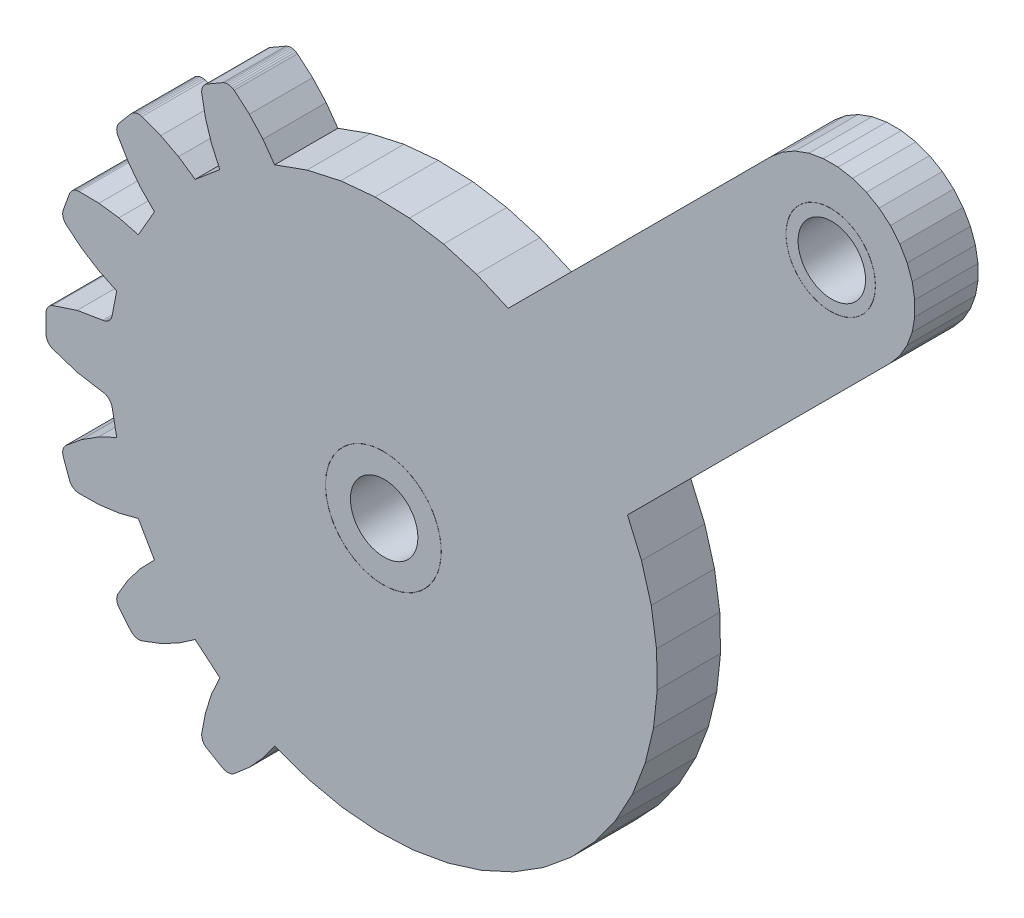
SolidWorks part; units mm, degrees
ref_plane "Front Plane" through (0, 0, 0) normal (0, 0, 1) x (1, 0, 0)
ref_plane "Top Plane" through (0, 0, 0) normal (0, 1, 0) x (1, 0, 0)
ref_plane "Right Plane" through (0, 0, 0) normal (1, 0, 0) x (0, 0, -1)
ref_plane "Plane1" through (0, 0, 3) normal (0, 0, 1) x (1, 0, 0)
sketch "Sketch1" plane through (0, 0, 3) normal (0, 0, 1) x (1, 0, 0)
  line L0 (41.2418, 13.6583) -> (41.2, 14.1358)
  line L1 (41.2, 14.1358) -> (41.2418, 14.6133)
  line L2 (41.2418, 14.6133) -> (41.3658, 15.0764)
  line L3 (41.3658, 15.0764) -> (41.5684, 15.5108)
  line L4 (41.5684, 15.5108) -> (41.8434, 15.9035)
  line L5 (41.8434, 15.9035) -> (42.1823, 16.2424)
  line L6 (42.1823, 16.2424) -> (42.575, 16.5174)
  line L7 (42.575, 16.5174) -> (43.0094, 16.72)
  line L8 (43.0094, 16.72) -> (43.4725, 16.844)
  line L9 (43.4725, 16.844) -> (43.95, 16.8858)
  line L10 (43.95, 16.8858) -> (44.4275, 16.844)
  line L11 (44.4275, 16.844) -> (44.8906, 16.72)
  line L12 (44.8906, 16.72) -> (45.325, 16.5174)
  line L13 (45.325, 16.5174) -> (45.7177, 16.2424)
  line L14 (45.7177, 16.2424) -> (46.0566, 15.9035)
  line L15 (46.0566, 15.9035) -> (46.3316, 15.5108)
  line L16 (46.3316, 15.5108) -> (46.5342, 15.0764)
  line L17 (46.5342, 15.0764) -> (46.6582, 14.6133)
  line L18 (46.6582, 14.6133) -> (46.7, 14.1358)
  line L19 (46.7, 14.1358) -> (46.6582, 13.6583)
  line L20 (46.6582, 13.6583) -> (46.5342, 13.1953)
  line L21 (46.5342, 13.1953) -> (46.3316, 12.7608)
  line L22 (46.3316, 12.7608) -> (46.0566, 12.3681)
  line L23 (46.0566, 12.3681) -> (45.7177, 12.0292)
  line L24 (45.7177, 12.0292) -> (45.325, 11.7542)
  line L25 (45.325, 11.7542) -> (44.8906, 11.5517)
  line L26 (44.8906, 11.5517) -> (44.4275, 11.4276)
  line L27 (44.4275, 11.4276) -> (43.95, 11.3858)
  line L28 (43.95, 11.3858) -> (43.4725, 11.4276)
  line L29 (43.4725, 11.4276) -> (43.0094, 11.5517)
  line L30 (43.0094, 11.5517) -> (42.575, 11.7542)
  line L31 (42.575, 11.7542) -> (42.1823, 12.0292)
  line L32 (42.1823, 12.0292) -> (41.8434, 12.3681)
  line L33 (41.8434, 12.3681) -> (41.5684, 12.7608)
  line L34 (41.5684, 12.7608) -> (41.3658, 13.1953)
  line L35 (41.3658, 13.1953) -> (41.2418, 13.6583)
  line L36 (30.938, 12.5267) -> (30.9937, 12.4646)
  line L37 (30.9937, 12.4646) -> (31.0383, 12.3942)
  line L38 (31.0383, 12.3942) -> (31.0705, 12.3173)
  line L39 (31.0705, 12.3173) -> (31.0896, 12.2361)
  line L40 (31.0896, 12.2361) -> (31.3026, 11.1288)
  line L41 (31.3026, 11.1288) -> (30.4429, 10.7165)
  line L42 (30.4429, 10.7165) -> (29.6383, 10.2049)
  line L43 (29.6383, 10.2049) -> (28.9004, 9.6011)
  line L44 (28.9004, 9.6011) -> (28.8438, 9.5394)
  line L45 (28.8438, 9.5394) -> (28.7983, 9.469)
  line L46 (28.7983, 9.469) -> (28.7652, 9.392)
  line L47 (28.7652, 9.392) -> (28.7454, 9.3106)
  line L48 (28.7454, 9.3106) -> (28.7395, 9.227)
  line L49 (28.7395, 9.227) -> (28.7477, 9.1436)
  line L50 (28.7477, 9.1436) -> (28.7696, 9.0627)
  line L51 (28.7696, 9.0627) -> (29.0602, 8.2643)
  line L52 (29.0602, 8.2643) -> (29.0954, 8.1882)
  line L53 (29.0954, 8.1882) -> (29.1427, 8.1191)
  line L54 (29.1427, 8.1191) -> (29.201, 8.0588)
  line L55 (29.201, 8.0588) -> (29.2685, 8.0092)
  line L56 (29.2685, 8.0092) -> (29.3433, 7.9715)
  line L57 (29.3433, 7.9715) -> (29.4234, 7.9468)
  line L58 (29.4234, 7.9468) -> (29.5065, 7.9358)
  line L59 (29.5065, 7.9358) -> (30.4599, 7.9477)
  line L60 (30.4599, 7.9477) -> (31.405, 8.0729)
  line L61 (31.405, 8.0729) -> (32.3286, 8.3097)
  line L62 (32.3286, 8.3097) -> (33.0938, 6.9844)
  line L63 (33.0938, 6.9844) -> (32.4269, 6.303)
  line L64 (32.4269, 6.303) -> (31.8459, 5.547)
  line L65 (31.8459, 5.547) -> (31.3589, 4.7273)
  line L66 (31.3589, 4.7273) -> (31.3269, 4.6499)
  line L67 (31.3269, 4.6499) -> (31.3082, 4.5682)
  line L68 (31.3082, 4.5682) -> (31.3034, 4.4846)
  line L69 (31.3034, 4.4846) -> (31.3127, 4.4013)
  line L70 (31.3127, 4.4013) -> (31.3357, 4.3207)
  line L71 (31.3357, 4.3207) -> (31.3719, 4.2451)
  line L72 (31.3719, 4.2451) -> (31.4202, 4.1766)
  line L73 (31.4202, 4.1766) -> (31.9664, 3.5258)
  line L74 (31.9664, 3.5258) -> (32.0254, 3.4663)
  line L75 (32.0254, 3.4663) -> (32.0936, 3.4176)
  line L76 (32.0936, 3.4176) -> (32.1689, 3.3809)
  line L77 (32.1689, 3.3809) -> (32.2493, 3.3573)
  line L78 (32.2493, 3.3573) -> (32.3325, 3.3474)
  line L79 (32.3325, 3.3474) -> (32.4162, 3.3517)
  line L80 (32.4162, 3.3517) -> (32.4981, 3.3698)
  line L81 (32.4981, 3.3698) -> (33.3899, 3.707)
  line L82 (33.3899, 3.707) -> (34.2352, 4.1479)
  line L83 (34.2352, 4.1479) -> (35.0221, 4.6863)
  line L84 (35.0221, 4.6863) -> (36.1944, 3.7027)
  line L85 (36.1944, 3.7027) -> (35.8008, 2.8342)
  line L86 (35.8008, 2.8342) -> (35.5134, 1.9252)
  line L87 (35.5134, 1.9252) -> (35.3361, 0.9883)
  line L88 (35.3361, 0.9883) -> (35.3325, 0.9046)
  line L89 (35.3325, 0.9046) -> (35.3429, 0.8215)
  line L90 (35.3429, 0.8215) -> (35.367, 0.7412)
  line L91 (35.367, 0.7412) -> (35.4042, 0.6661)
  line L92 (35.4042, 0.6661) -> (35.4534, 0.5983)
  line L93 (35.4534, 0.5983) -> (35.5133, 0.5396)
  line L94 (35.5133, 0.5396) -> (35.5821, 0.4918)
  line L95 (35.5821, 0.4918) -> (36.3179, 0.067)
  line L96 (36.3179, 0.067) -> (36.3937, 0.0313)
  line L97 (36.3937, 0.0313) -> (36.4745, 0.0088)
  line L98 (36.4745, 0.0088) -> (36.5578, 0.0001)
  line L99 (36.5578, 0.0001) -> (36.6414, 0.0054)
  line L100 (36.6414, 0.0054) -> (36.723, 0.0247)
  line L101 (36.723, 0.0247) -> (36.8002, 0.0572)
  line L102 (36.8002, 0.0572) -> (36.8709, 0.1022)
  line L103 (36.8709, 0.1022) -> (37.5936, 0.7242)
  line L104 (37.5936, 0.7242) -> (38.2371, 1.4276)
  line L105 (38.2371, 1.4276) -> (38.7925, 2.2027)
  line L106 (38.7925, 2.2027) -> (40.3707, 1.6383)
  line L107 (40.3707, 1.6383) -> (42.0084, 1.2816)
  line L108 (42.0084, 1.2816) -> (43.6784, 1.1386)
  line L109 (43.6784, 1.1386) -> (45.3529, 1.2117)
  line L110 (45.3529, 1.2117) -> (47.0041, 1.4996)
  line L111 (47.0041, 1.4996) -> (48.6045, 1.9976)
  line L112 (48.6045, 1.9976) -> (50.1275, 2.6974)
  line L113 (50.1275, 2.6974) -> (51.5479, 3.5872)
  line L114 (51.5479, 3.5872) -> (52.8419, 4.6525)
  line L115 (52.8419, 4.6525) -> (53.9882, 5.8754)
  line L116 (53.9882, 5.8754) -> (54.9676, 7.2356)
  line L117 (54.9676, 7.2356) -> (55.7638, 8.7105)
  line L118 (55.7638, 8.7105) -> (56.3636, 10.2755)
  line L119 (56.3636, 10.2755) -> (56.7571, 11.9048)
  line L120 (56.7571, 11.9048) -> (56.9377, 13.5711)
  line L121 (56.9377, 13.5711) -> (56.9024, 15.2469)
  line L122 (56.9024, 15.2469) -> (56.6518, 16.9041)
  line L123 (56.6518, 16.9041) -> (56.1901, 18.5154)
  line L124 (56.1901, 18.5154) -> (55.5249, 20.0538)
  line L125 (55.5249, 20.0538) -> (67.9916, 32.5206)
  line L126 (67.9916, 32.5206) -> (68.4398, 33.0547)
  line L127 (68.4398, 33.0547) -> (68.7884, 33.6585)
  line L128 (68.7884, 33.6585) -> (69.0269, 34.3137)
  line L129 (69.0269, 34.3137) -> (69.148, 35.0004)
  line L130 (69.148, 35.0004) -> (69.148, 35.6976)
  line L131 (69.148, 35.6976) -> (69.0269, 36.3843)
  line L132 (69.0269, 36.3843) -> (68.7884, 37.0395)
  line L133 (68.7884, 37.0395) -> (68.4398, 37.6433)
  line L134 (68.4398, 37.6433) -> (67.9916, 38.1774)
  line L135 (67.9916, 38.1774) -> (67.4575, 38.6256)
  line L136 (67.4575, 38.6256) -> (66.8537, 38.9742)
  line L137 (66.8537, 38.9742) -> (66.1985, 39.2127)
  line L138 (66.1985, 39.2127) -> (65.5118, 39.3338)
  line L139 (65.5118, 39.3338) -> (64.8146, 39.3338)
  line L140 (64.8146, 39.3338) -> (64.1279, 39.2127)
  line L141 (64.1279, 39.2127) -> (63.4727, 38.9742)
  line L142 (63.4727, 38.9742) -> (62.8689, 38.6256)
  line L143 (62.8689, 38.6256) -> (62.3348, 38.1774)
  line L144 (62.3348, 38.1774) -> (49.868, 25.7107)
  line L145 (49.868, 25.7107) -> (48.369, 26.3617)
  line L146 (48.369, 26.3617) -> (46.8001, 26.8195)
  line L147 (46.8001, 26.8195) -> (45.1862, 27.0769)
  line L148 (45.1862, 27.0769) -> (43.5528, 27.1297)
  line L149 (43.5528, 27.1297) -> (41.9256, 26.9772)
  line L150 (41.9256, 26.9772) -> (40.3304, 26.6217)
  line L151 (40.3304, 26.6217) -> (38.7925, 26.0689)
  line L152 (38.7925, 26.0689) -> (38.2371, 26.844)
  line L153 (38.2371, 26.844) -> (37.5936, 27.5475)
  line L154 (37.5936, 27.5475) -> (36.8709, 28.1694)
  line L155 (36.8709, 28.1694) -> (36.8002, 28.2144)
  line L156 (36.8002, 28.2144) -> (36.723, 28.247)
  line L157 (36.723, 28.247) -> (36.6414, 28.2662)
  line L158 (36.6414, 28.2662) -> (36.5578, 28.2715)
  line L159 (36.5578, 28.2715) -> (36.4745, 28.2628)
  line L160 (36.4745, 28.2628) -> (36.3937, 28.2403)
  line L161 (36.3937, 28.2403) -> (36.3179, 28.2046)
  line L162 (36.3179, 28.2046) -> (35.5821, 27.7798)
  line L163 (35.5821, 27.7798) -> (35.5133, 27.732)
  line L164 (35.5133, 27.732) -> (35.4534, 27.6733)
  line L165 (35.4534, 27.6733) -> (35.4042, 27.6055)
  line L166 (35.4042, 27.6055) -> (35.367, 27.5304)
  line L167 (35.367, 27.5304) -> (35.3429, 27.4501)
  line L168 (35.3429, 27.4501) -> (35.3325, 27.367)
  line L169 (35.3325, 27.367) -> (35.3361, 27.2833)
  line L170 (35.3361, 27.2833) -> (35.5134, 26.3465)
  line L171 (35.5134, 26.3465) -> (35.8008, 25.4374)
  line L172 (35.8008, 25.4374) -> (36.1944, 24.5689)
  line L173 (36.1944, 24.5689) -> (35.0221, 23.5853)
  line L174 (35.0221, 23.5853) -> (34.2352, 24.1237)
  line L175 (34.2352, 24.1237) -> (33.3899, 24.5646)
  line L176 (33.3899, 24.5646) -> (32.4981, 24.9018)
  line L177 (32.4981, 24.9018) -> (32.4162, 24.92)
  line L178 (32.4162, 24.92) -> (32.3325, 24.9242)
  line L179 (32.3325, 24.9242) -> (32.2493, 24.9143)
  line L180 (32.2493, 24.9143) -> (32.1689, 24.8907)
  line L181 (32.1689, 24.8907) -> (32.0936, 24.8541)
  line L182 (32.0936, 24.8541) -> (32.0254, 24.8053)
  line L183 (32.0254, 24.8053) -> (31.9664, 24.7458)
  line L184 (31.9664, 24.7458) -> (31.4202, 24.095)
  line L185 (31.4202, 24.095) -> (31.3719, 24.0265)
  line L186 (31.3719, 24.0265) -> (31.3357, 23.9509)
  line L187 (31.3357, 23.9509) -> (31.3127, 23.8703)
  line L188 (31.3127, 23.8703) -> (31.3034, 23.7871)
  line L189 (31.3034, 23.7871) -> (31.3082, 23.7034)
  line L190 (31.3082, 23.7034) -> (31.3269, 23.6217)
  line L191 (31.3269, 23.6217) -> (31.3589, 23.5443)
  line L192 (31.3589, 23.5443) -> (31.8459, 22.7246)
  line L193 (31.8459, 22.7246) -> (32.4269, 21.9686)
  line L194 (32.4269, 21.9686) -> (33.0938, 21.2872)
  line L195 (33.0938, 21.2872) -> (32.3286, 19.9619)
  line L196 (32.3286, 19.9619) -> (31.405, 20.1987)
  line L197 (31.405, 20.1987) -> (30.4599, 20.3239)
  line L198 (30.4599, 20.3239) -> (29.5065, 20.3358)
  line L199 (29.5065, 20.3358) -> (29.4234, 20.3248)
  line L200 (29.4234, 20.3248) -> (29.3433, 20.3001)
  line L201 (29.3433, 20.3001) -> (29.2685, 20.2624)
  line L202 (29.2685, 20.2624) -> (29.201, 20.2128)
  line L203 (29.201, 20.2128) -> (29.1427, 20.1525)
  line L204 (29.1427, 20.1525) -> (29.0954, 20.0834)
  line L205 (29.0954, 20.0834) -> (29.0602, 20.0073)
  line L206 (29.0602, 20.0073) -> (28.7696, 19.2089)
  line L207 (28.7696, 19.2089) -> (28.7477, 19.1281)
  line L208 (28.7477, 19.1281) -> (28.7395, 19.0447)
  line L209 (28.7395, 19.0447) -> (28.7454, 18.9611)
  line L210 (28.7454, 18.9611) -> (28.7652, 18.8796)
  line L211 (28.7652, 18.8796) -> (28.7983, 18.8026)
  line L212 (28.7983, 18.8026) -> (28.8438, 18.7323)
  line L213 (28.8438, 18.7323) -> (28.9004, 18.6705)
  line L214 (28.9004, 18.6705) -> (29.6383, 18.0668)
  line L215 (29.6383, 18.0668) -> (30.4429, 17.5551)
  line L216 (30.4429, 17.5551) -> (31.3026, 17.1428)
  line L217 (31.3026, 17.1428) -> (31.0896, 16.0355)
  line L218 (31.0896, 16.0355) -> (31.0705, 15.9543)
  line L219 (31.0705, 15.9543) -> (31.0383, 15.8774)
  line L220 (31.0383, 15.8774) -> (30.9937, 15.807)
  line L221 (30.9937, 15.807) -> (30.938, 15.7449)
  line L222 (30.938, 15.7449) -> (30.8728, 15.6929)
  line L223 (30.8728, 15.6929) -> (30.7998, 15.6525)
  line L224 (30.7998, 15.6525) -> (30.7212, 15.6248)
  line L225 (30.7212, 15.6248) -> (30.639, 15.6106)
  line L226 (30.639, 15.6106) -> (29.4253, 15.4081)
  line L227 (29.4253, 15.4081) -> (28.257, 15.0219)
  line L228 (28.257, 15.0219) -> (28.1827, 14.9832)
  line L229 (28.1827, 14.9832) -> (28.1159, 14.9326)
  line L230 (28.1159, 14.9326) -> (28.0585, 14.8716)
  line L231 (28.0585, 14.8716) -> (28.012, 14.8018)
  line L232 (28.012, 14.8018) -> (27.9779, 14.7253)
  line L233 (27.9779, 14.7253) -> (27.957, 14.6441)
  line L234 (27.957, 14.6441) -> (27.95, 14.5606)
  line L235 (27.95, 14.5606) -> (27.95, 13.711)
  line L236 (27.95, 13.711) -> (27.957, 13.6275)
  line L237 (27.957, 13.6275) -> (27.9779, 13.5463)
  line L238 (27.9779, 13.5463) -> (28.012, 13.4698)
  line L239 (28.012, 13.4698) -> (28.0585, 13.4)
  line L240 (28.0585, 13.4) -> (28.1159, 13.339)
  line L241 (28.1159, 13.339) -> (28.1827, 13.2884)
  line L242 (28.1827, 13.2884) -> (28.257, 13.2497)
  line L243 (28.257, 13.2497) -> (29.4253, 12.8635)
  line L244 (29.4253, 12.8635) -> (30.639, 12.6611)
  line L245 (30.639, 12.6611) -> (30.7212, 12.6468)
  line L246 (30.7212, 12.6468) -> (30.7998, 12.6191)
  line L247 (30.7998, 12.6191) -> (30.8728, 12.5787)
  line L248 (30.8728, 12.5787) -> (30.938, 12.5267)
  line L249 (65.89, 33.3522) -> (65.5322, 33.2563)
  line L250 (65.5322, 33.2563) -> (65.1632, 33.224)
  line L251 (65.1632, 33.224) -> (64.7942, 33.2563)
  line L252 (64.7942, 33.2563) -> (64.4364, 33.3522)
  line L253 (64.4364, 33.3522) -> (64.1007, 33.5087)
  line L254 (64.1007, 33.5087) -> (63.7973, 33.7212)
  line L255 (63.7973, 33.7212) -> (63.5354, 33.9831)
  line L256 (63.5354, 33.9831) -> (63.3229, 34.2865)
  line L257 (63.3229, 34.2865) -> (63.1664, 34.6222)
  line L258 (63.1664, 34.6222) -> (63.0705, 34.98)
  line L259 (63.0705, 34.98) -> (63.0382, 35.349)
  line L260 (63.0382, 35.349) -> (63.0705, 35.718)
  line L261 (63.0705, 35.718) -> (63.1664, 36.0758)
  line L262 (63.1664, 36.0758) -> (63.3229, 36.4115)
  line L263 (63.3229, 36.4115) -> (63.5354, 36.7149)
  line L264 (63.5354, 36.7149) -> (63.7973, 36.9769)
  line L265 (63.7973, 36.9769) -> (64.1007, 37.1893)
  line L266 (64.1007, 37.1893) -> (64.4364, 37.3459)
  line L267 (64.4364, 37.3459) -> (64.7942, 37.4417)
  line L268 (64.7942, 37.4417) -> (65.1632, 37.474)
  line L269 (65.1632, 37.474) -> (65.5322, 37.4417)
  line L270 (65.5322, 37.4417) -> (65.89, 37.3459)
  line L271 (65.89, 37.3459) -> (66.2257, 37.1893)
  line L272 (66.2257, 37.1893) -> (66.5291, 36.9769)
  line L273 (66.5291, 36.9769) -> (66.7911, 36.7149)
  line L274 (66.7911, 36.7149) -> (67.0035, 36.4115)
  line L275 (67.0035, 36.4115) -> (67.16, 36.0758)
  line L276 (67.16, 36.0758) -> (67.2559, 35.718)
  line L277 (67.2559, 35.718) -> (67.2882, 35.349)
  line L278 (67.2882, 35.349) -> (67.2559, 34.98)
  line L279 (67.2559, 34.98) -> (67.16, 34.6222)
  line L280 (67.16, 34.6222) -> (67.0035, 34.2865)
  line L281 (67.0035, 34.2865) -> (66.7911, 33.9831)
  line L282 (66.7911, 33.9831) -> (66.5291, 33.7212)
  line L283 (66.5291, 33.7212) -> (66.2257, 33.5087)
  line L284 (66.2257, 33.5087) -> (65.89, 33.3522)
extrude "Boss-Extrude1" add sketch "Sketch1" against normal blind 3
sketch "Sketch2" plane through (0, 0, 3) normal (0, 0, 1) x (1, 0, 0)
  line L0 (45.8871, 16.073) -> (42.0129, 12.1987) construction
  line L1 (46.0566, 15.9035) -> (45.7177, 16.2424) construction
  line L2 (41.8434, 12.3681) -> (42.1823, 12.0292) construction
  circle A0 centre (43.95, 14.1358) radius 2.7395
extrude "Boss-Extrude2" add sketch "Sketch2" against normal blind 3 separate body
hole_wizard "M3 Clearance Hole1" positions "Sketch3" profile "Sketch4" hole size "M3" standard "ANSI Metric" end condition through all
sketch "Sketch3" plane through (0, 0, 3) normal (0, 0, 1) x (1, 0, 0)
  point P0 (43.9856, 14.1495)
sketch "Sketch4" plane through (43.9856, 14.1495, 3) normal (1, 0, 0) x (0, -1, 0)
  line L0 (0, 0) -> (0, 3)
  line L1 (0, 3) -> (1.6, 3)
  line L2 (1.6, 3) -> (1.6, 0)
  line L5 (1.6, 0) -> (0, 0)
  line L11 (0, -6.35) -> (0, 107.95) construction
  dimension "Thru Hole Dia." = 3.2
  dimension "Thru Hole Depth" = 3
sketch "Sketch5" plane through (0, 0, 3) normal (0, 0, 1) x (1, 0, 0)
  line L0 (66.8973, 36.5632) -> (63.4291, 34.1348) construction
  line L1 (67.0035, 36.4115) -> (66.7911, 36.7149) construction
  line L2 (63.3229, 34.2865) -> (63.5354, 33.9831) construction
  circle A0 centre (65.1632, 35.349) radius 2.1169
extrude "Boss-Extrude3" add sketch "Sketch5" against normal blind 3 separate body
hole_wizard "M3 Clearance Hole2" positions "Sketch6" profile "Sketch7" hole size "M3" standard "ANSI Metric" end condition through all
sketch "Sketch6" plane through (0, 0, 3) normal (0, 0, 1) x (1, 0, 0)
  point P0 (65.2142, 35.3568)
sketch "Sketch7" plane through (65.2142, 35.3568, 3) normal (1, 0, 0) x (0, -1, 0)
  line L0 (0, 0) -> (0, 3)
  line L1 (0, 3) -> (1.6, 3)
  line L2 (1.6, 3) -> (1.6, 0)
  line L5 (1.6, 0) -> (0, 0)
  line L11 (0, -6.35) -> (0, 107.95) construction
  dimension "Thru Hole Dia." = 3.2
  dimension "Thru Hole Depth" = 3
